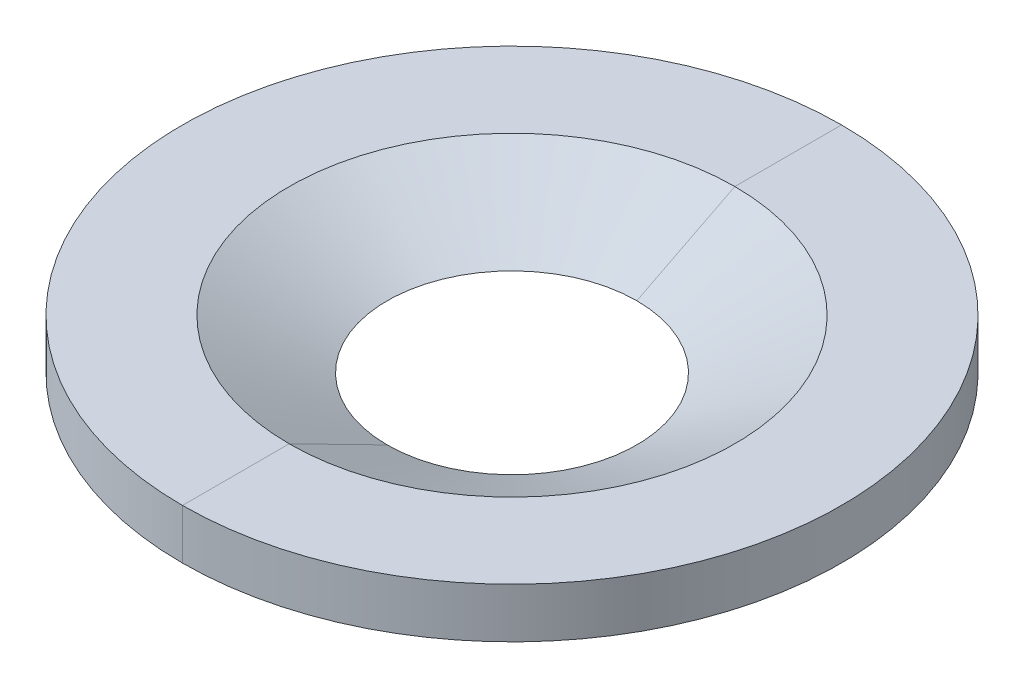
SolidWorks part; units mm, degrees
ref_plane "Front Plane" through (0, 0, 0) normal (0, 0, 1) x (1, 0, 0)
ref_plane "Top Plane" through (0, 0, 0) normal (0, 1, 0) x (1, 0, 0)
ref_plane "Right Plane" through (0, 0, 0) normal (1, 0, 0) x (0, 0, -1)
sketch "Sketch1" plane through (0, 0, 0) normal (0, 1, 0) x (1, 0, 0)
  circle A0 centre (0, 0) radius 83.82
  circle A1 centre (0, 0) radius 31.75
  dimension "D1" = 167.64
  dimension "D2" = 63.5
extrude "Boss-Extrude1" add sketch "Sketch1" along normal mid plane 12.7
sketch "Sketch4" plane through (0, 0, 0) normal (0, 0, 1) x (1, 0, 0)
  line L0 (0, 23.2786) -> (0, -14.9525) construction
sketch "Sketch3" plane through (0, 0, 0) normal (0, 0, 1) x (1, 0, 0)
  line L0 (-31.75, -6.35) -> (-56.6752, 6.35)
  line L1 (83.82, 6.35) -> (-83.82, 6.35) construction
  line L2 (-56.6752, 6.35) -> (-31.75, 6.35)
  line L3 (-31.75, 6.35) -> (-31.75, -6.35)
  point P7 (0, 0)
  dimension "D1" = 27
revolve "Cut-Revolve1" cut sketch "Sketch3" angle 360 about L0
split "Split1" trim tools "Right Plane" bodies to split 103 resulting bodies 104 105
